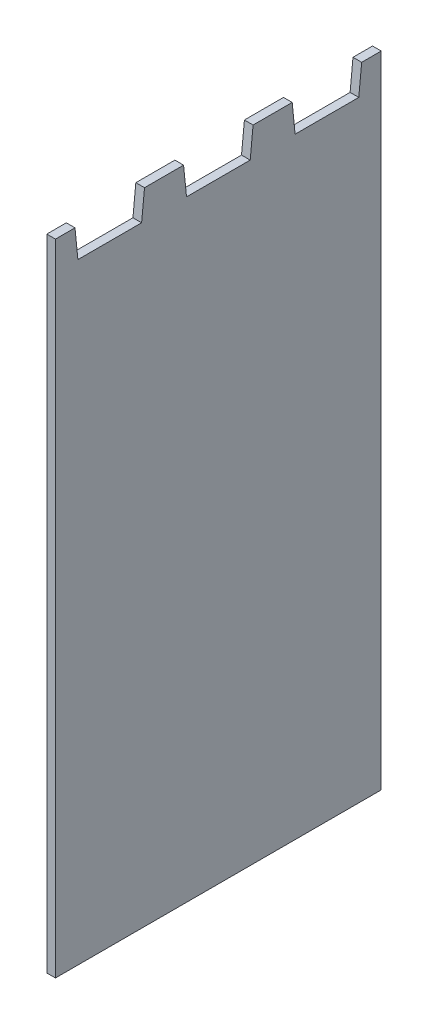
SolidWorks part; units mm, degrees
ref_plane "Front Plane" through (0, 0, 0) normal (0, 0, 1) x (1, 0, 0)
ref_plane "Top Plane" through (0, 0, 0) normal (0, 1, 0) x (1, 0, 0)
ref_plane "Right Plane" through (0, 0, 0) normal (1, 0, 0) x (0, 0, -1)
sketch "Sketch2" plane through (0, 0, 0) normal (1, 0, 0) x (0, 0, -1)
  line L0 (-18.75, 103) -> (-18.75, 118)
  line L1 (-18.75, -103) -> (18.75, -103)
  line L2 (-18.75, -103) -> (-18.75, 103)
  line L3 (-18.75, 103) -> (18.75, 103)
  line L4 (18.75, -103) -> (18.75, 103)
  line L5 (-18.75, -103) -> (18.75, 103) construction
  line L6 (-18.75, 103) -> (18.75, -103) construction
  line L7 (-18.75, 118) -> (-12, 118)
  line L8 (-12, 118) -> (-11, 108)
  line L9 (-11, 108) -> (11, 108)
  line L10 (11, 108) -> (12, 118)
  line L11 (12, 118) -> (18.75, 118)
  line L12 (18.75, 118) -> (18.75, 103)
  line L13 (-12, 118) -> (-12, 108) construction
  line L14 (-12, 108) -> (-11, 108) construction
  line L15 (11, 108) -> (12, 108) construction
  line L16 (12, 108) -> (12, 118) construction
  line L17 (-18.75, 118) -> (-18.75, 125) construction
  line L18 (-18.75, 125) -> (18.75, 125) construction
  line L19 (18.75, 125) -> (18.75, 118) construction
  point P0 (0, 0)
  dimension "D1" = 206
  dimension "D2" = 37.5
  dimension "D3" = 22
  dimension "D4" = 10
  dimension "D5" = 1
  dimension "D6" = 7
  dimension "D7" = 228
extrude "Boss-Extrude2" add sketch "Sketch2" along normal blind 3 contours L1 L4 L3 L2 | L12 L11 L10 L9 L8 L7 L0 L3
pattern_linear "LPattern1" count 3 spacing 37.5 along (0, 0, 1) of "Boss-Extrude2"
